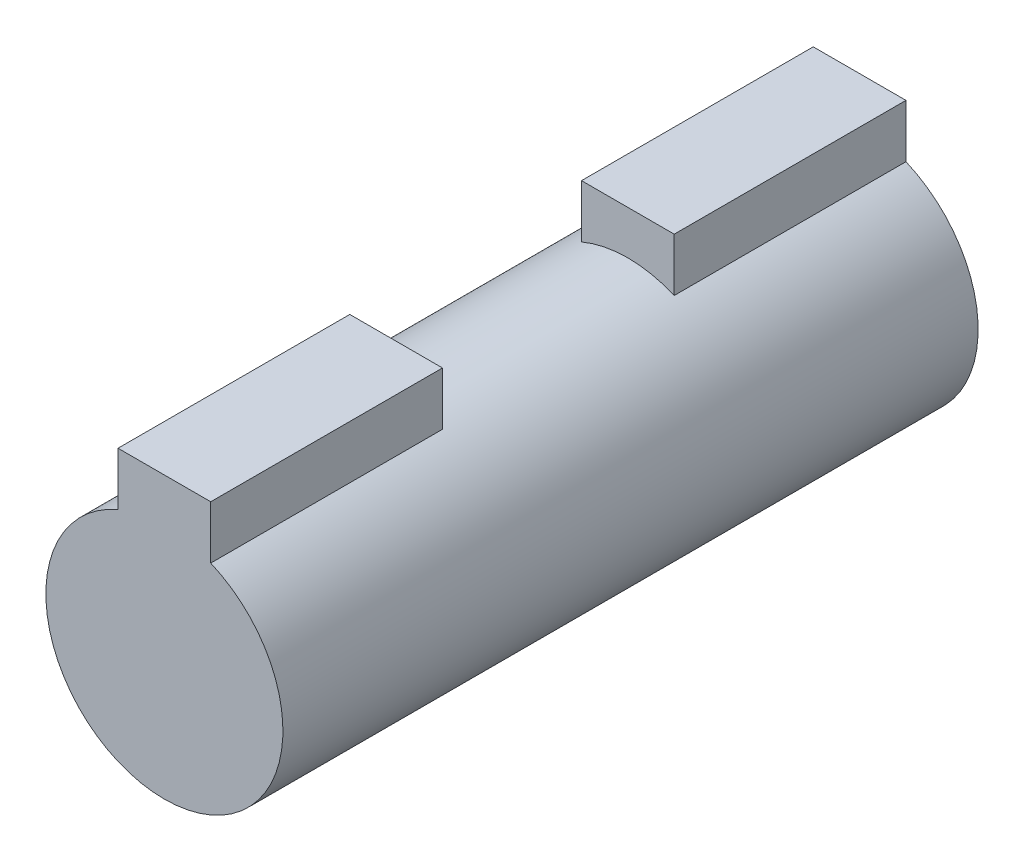
SolidWorks part; units mm, degrees
ref_plane "Front Plane" through (0, 0, 0) normal (0, 0, 1) x (1, 0, 0)
ref_plane "Top Plane" through (0, 0, 0) normal (0, 1, 0) x (1, 0, 0)
ref_plane "Right Plane" through (0, 0, 0) normal (1, 0, 0) x (0, 0, -1)
sketch "Sketch1" plane through (0, 0, 0) normal (0, 0, 1) x (1, 0, 0)
  line L0 (0, 0) -> (0, 5.1145) construction
  line L2 (-2, 7) -> (2, 7)
  line L3 (-2, 7) -> (-2, 4.7072)
  line L5 (2, 7) -> (2, 4.7072)
  arc A0 (-2, 4.7072) -> (2, 4.7072) centre (0, 0) ccw
  point P3 (0, 5.677)
  dimension "D1" = 10.229
  dimension "D2" = 4
  dimension "D3" = 7
  dimension "D4" = 5.677
extrude "Boss-Extrude1" add sketch "Sketch1" along normal blind 30
sketch "Sketch2" plane through (0, 0, 30) normal (0, 0, 1) x (1, 0, 0)
  circle A0 centre (0, 0) radius 5.1145
  circle A1 centre (0, 0) radius 9.0681
extrude "Cut-Extrude2" cut sketch "Sketch2" against normal blind 10 from offset 10 offset against normal yes
